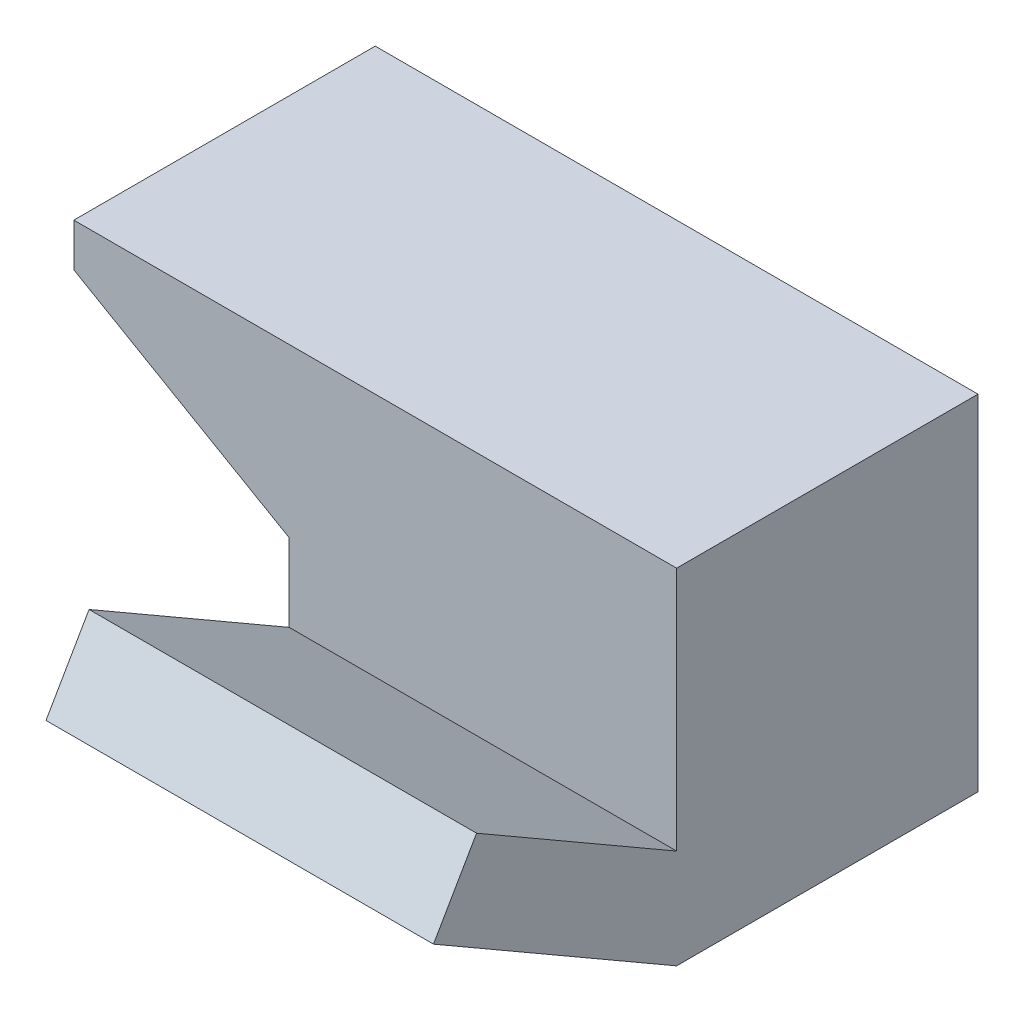
SolidWorks part; units mm, degrees
ref_plane "Front Plane" through (0, 0, 0) normal (0, 0, 1) x (1, 0, 0)
ref_plane "Top Plane" through (0, 0, 0) normal (0, 1, 0) x (1, 0, 0)
ref_plane "Right Plane" through (0, 0, 0) normal (1, 0, 0) x (0, 0, -1)
sketch "Sketch1" plane through (0, 0, 0) normal (0, 1, 0) x (1, 0, 0)
  line L0 (57.15, 0) -> (88.9, 0)
  line L1 (0, 0) -> (57.15, 0)
  line L2 (0, 0) -> (0, 50.8)
  line L3 (0, 50.8) -> (57.15, 50.8)
  line L4 (57.15, 24.6809) -> (57.15, 50.8)
  line L5 (88.9, 0) -> (88.9, 6.35)
  line L6 (88.9, 6.35) -> (57.15, 24.6809)
  dimension "D1" = 50.8
  dimension "D2" = 57.15
  dimension "D3" = 31.75
  dimension "D4" = 6.35
  dimension "D5" = 60
  dimension "D6" = 57.15
extrude "Boss-Extrude1" add sketch "Sketch1" along normal blind 44.45
sketch "Sketch3" plane through (24.9746, 0, -43.2573) normal (0.5, 0, -0.866) x (-0.866, 0, -0.5)
  line L0 (-73.8147, 0) -> (-37.1529, 0) construction
  line L1 (-73.8147, 44.45) -> (-73.8147, 0) construction
  circle A0 centre (-54.7647, 22.352) radius 9.525
  dimension "D1" = 22.352
  dimension "D3" = 19.05
  dimension "D2" = 19.05
extrude "Cut-Extrude1" cut sketch "Sketch3" against normal blind 6.35
sketch "Sketch4" plane through (0, 0, 0) normal (-1, 0, 0) x (0, 0, 1)
  line L0 (-50.8, 44.45) -> (-30.099, 80.3052)
  line L2 (-19.1005, 73.9552) -> (-36.1353, 44.45)
  line L3 (-50.8, 44.45) -> (0, 44.45) construction
  line L4 (-50.8, 44.45) -> (-50.8, 0) construction
  line L5 (-30.099, 80.3052) -> (-19.1005, 73.9552)
  line L9 (-50.8, 0) -> (0, 0)
  line L10 (0, 0) -> (0, 44.45)
  line L11 (0, 44.45) -> (-50.8, 44.45)
  line L12 (-50.8, 44.45) -> (-50.8, 0)
  line L13 (-50.8, 0) -> (0, 0)
  line L14 (0, 0) -> (0, 44.45)
  line L15 (0, 44.45) -> (-36.1353, 44.45)
  line L16 (-50.8, 44.45) -> (-50.8, 0)
  dimension "D1" = 30
  dimension "D2" = 12.7
  dimension "D3" = 41.402
  dimension "D4" = 60
  dimension "D5" = 0
extrude "Boss-Extrude2" add sketch "Sketch4" against normal blind 57.15
sketch "Sketch5" plane through (0, 33.1095, -57.3474) normal (0, 0.5, -0.866) x (-1, 0, 0)
  line L0 (-57.15, 13.0948) -> (0, 13.0948) construction
  line L1 (0, 54.4968) -> (0, 13.0948) construction
  circle A0 centre (-28.702, 35.4468) radius 9.525
  dimension "D3" = 19.05
  dimension "D1" = 22.352
  dimension "D2" = 28.702
extrude "Cut-Extrude2" cut sketch "Sketch5" against normal blind 6.35
sketch "Sketch6" plane through (0, 0, -50.8) normal (0, 0, -1) x (-1, 0, 0)
  line L0 (-57.15, 44.45) -> (-57.15, 0) construction
  line L1 (-57.15, 44.45) -> (0, 44.45) construction
  line L2 (0, 44.45) -> (0, 0) construction
  line L3 (-57.15, 0) -> (0, 0) construction
  circle A0 centre (-41.148, 31.75) radius 4.7625
  circle A1 centre (-16.002, 31.75) radius 4.7625
  circle A2 centre (-16.002, 12.7) radius 4.7625
  circle A3 centre (-41.148, 12.7) radius 4.7625
  dimension "D1" = 9.525
  dimension "D6" = 16.002
  dimension "D7" = 12.7
  dimension "D2" = 16.002
  dimension "D3" = 12.7
  dimension "D8" = 19.05
  dimension "D4" = 2
  dimension "D5" = 2
extrude "Cut-Extrude3" cut sketch "Sketch6" against normal blind 12.7
move or copy body "Body-Move/Copy1" bodies to move or copy 105 copy no rotation origin (44.45, 32.7763, -32.7763) rotation axis (0, 0.7071, 0.7071) rotation angle 180
